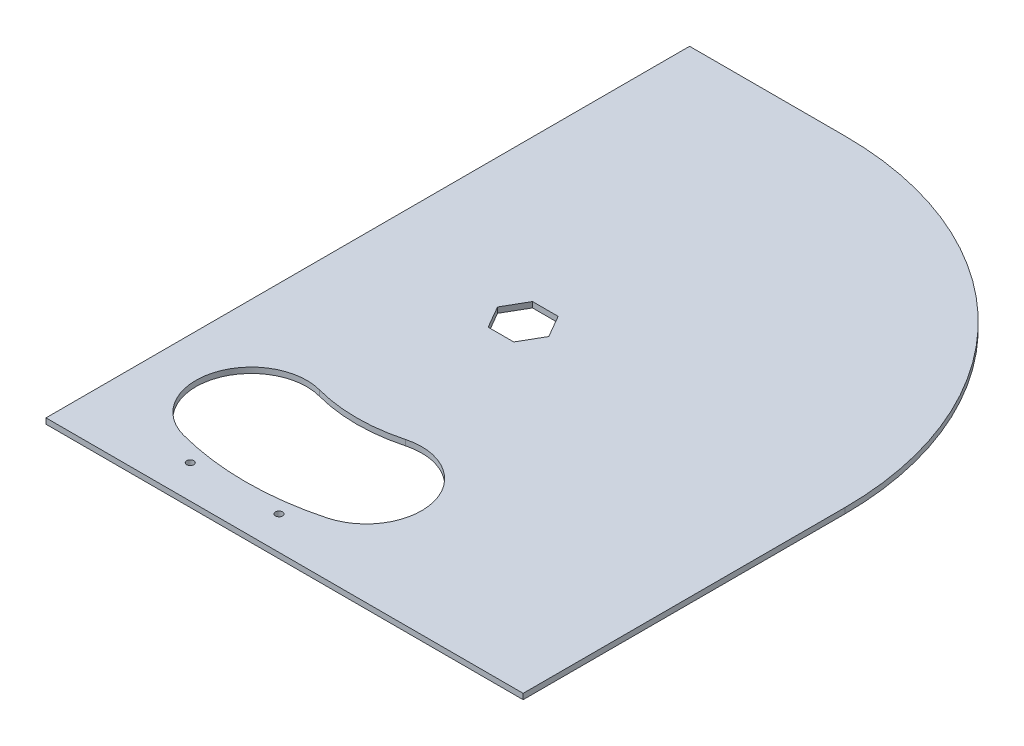
SolidWorks part; units mm, degrees
material "Acrylic (Medium-high impact)"
ref_plane "Front Plane" through (0, 0, 0) normal (0, 0, 1) x (1, 0, 0)
ref_plane "Top Plane" through (0, 0, 0) normal (0, 1, 0) x (1, 0, 0)
ref_plane "Right Plane" through (0, 0, 0) normal (1, 0, 0) x (0, 0, -1)
sketch "Sketch1" plane through (0, 0, 0) normal (0, 1, 0) x (1, 0, 0)
  line L0 (0, 145) -> (145, 145) construction
  line L1 (0, 0) -> (-70, 0)
  line L2 (0, 0) -> (0, 290) construction
  line L3 (0, 290) -> (-70, 290)
  line L4 (-70, 0) -> (-70, 290)
  line L5 (145, 145) -> (145, 0)
  line L6 (145, 0) -> (0, 0)
  arc A0 (0, 290) -> (145, 145) centre (0, 145) cw
  circle A1 centre (0, 250) radius 20 construction
  circle A2 centre (0, 250) radius 25 construction
  point P7 (0, 145)
  point P11 (0, 270)
  point P12 (-20, 250)
  dimension "D2" = 40
  dimension "D5" = 50
  dimension "D1" = 290
  dimension "D3" = 105
  dimension "D4" = 50
sketch "Sketch2" plane through (0, 0, 0) normal (0, 1, 0) x (1, 0, 0)
  line L0 (0, 0) -> (0, 290) construction
  line L1 (-27.5, 250) -> (27.5, 250) construction
  line L2 (-27.5, 250) -> (-27.5, 217.5)
  line L3 (-27.5, 217.5) -> (27.5, 217.5)
  line L4 (27.5, 250) -> (27.5, 217.5)
  line L5 (-27.5, 250) -> (27.5, 217.5) construction
  line L6 (-27.5, 217.5) -> (27.5, 250) construction
  arc A0 (-27.5, 250) -> (27.5, 250) centre (0, 250) cw
  point P0 (0, 233.75)
  dimension "D1" = 27.5
  dimension "D2" = 32.5
sketch "Sketch3" plane through (0, 0, 0) normal (0, 1, 0) x (1, 0, 0)
  line L0 (0, 0) -> (0, 290) construction
  circle A0 centre (0, 40) radius 26.25
  dimension "D2" = 52.5
  dimension "D1" = 105
extrude "Boss-Extrude2" add sketch "Sketch1" along normal blind 2.5
extrude "Cut-Extrude2" [suppressed] cut sketch "Sketch2" along normal through all
extrude "Cut-Extrude3" [suppressed] cut sketch "Sketch3" along normal through all
sketch "Sketch4" [suppressed] plane through (0, 0, 0) normal (0, 1, 0) x (1, 0, 0)
  line L0 (0, 217.5) -> (0, 209.5) construction
  line L1 (-27.5, 217.5) -> (27.5, 217.5) construction
  line L2 (-12.5, 209.5) -> (12.5, 209.5) construction
  circle A0 centre (12.5, 209.5) radius 1.6
  circle A1 centre (-12.5, 209.5) radius 1.6
  dimension "D2" = 3.2
  dimension "D1" = 8
  dimension "D3" = 25
extrude "Cut-Extrude4" [suppressed] cut sketch "Sketch4" along normal blind 10
sketch "Sketch6" plane through (0, 0, 0) normal (0, 1, 0) x (1, 0, 0)
  line L1 (0, 0) -> (0, 290) construction
  line L2 (5.7735, 135) -> (11.547, 145)
  line L3 (11.547, 145) -> (5.7735, 155)
  line L4 (5.7735, 155) -> (-5.7735, 155)
  line L5 (-5.7735, 155) -> (-11.547, 145)
  line L6 (-11.547, 145) -> (-5.7735, 135)
  line L7 (-5.7735, 135) -> (5.7735, 135)
  arc A0 (145, 145) -> (0, 290) centre (0, 145) ccw construction
  circle A2 centre (0, 145) radius 10 construction
  point P1 (0, 145)
  dimension "D1" = 20
extrude "Cut-Extrude5" cut sketch "Sketch6" along normal through all
sketch "Sketch7" plane through (0, 0, 0) normal (0, 1, 0) x (1, 0, 0)
  line L0 (-11.547, 145) -> (11.547, 145) construction
  line L2 (0, 145) -> (0, 45) construction
  line L3 (0, 145) -> (25.8819, 48.4074) construction
  line L4 (0, 145) -> (-25.8819, 48.4074) construction
  arc A0 (-25.8819, 48.4074) -> (25.8819, 48.4074) centre (0, 145) ccw construction
  arc A1 (-32.3524, 24.2593) -> (32.3524, 24.2593) centre (0, 145) ccw
  arc A2 (-19.4114, 72.5556) -> (19.4114, 72.5556) centre (0, 145) ccw
  arc A3 (-19.4114, 72.5556) -> (-32.3524, 24.2593) centre (-25.8819, 48.4074) ccw
  arc A4 (32.3524, 24.2593) -> (19.4114, 72.5556) centre (25.8819, 48.4074) ccw
  point P0 (0, 145)
  point P5 (0, 145)
  point P10 (0, 45)
  dimension "D1" = 50
  dimension "D2" = 100
  dimension "D3" = 15
extrude "Cut-Extrude7" cut sketch "Sketch7" along normal through all
sketch "Sketch8" plane through (0, 0, 0) normal (0, 1, 0) x (1, 0, 0)
  line L0 (0, 0) -> (0, 290) construction
  circle A0 centre (-20, 15) radius 1.6
  arc A1 (-32.3524, 24.2593) -> (32.3524, 24.2593) centre (0, 145) ccw construction
  circle A2 centre (20, 15) radius 1.6
  point P6 (0, 20)
  dimension "D1" = 3.2
  dimension "D2" = 5
  dimension "D3" = 40
extrude "Cut-Extrude8" cut sketch "Sketch8" along normal through all
